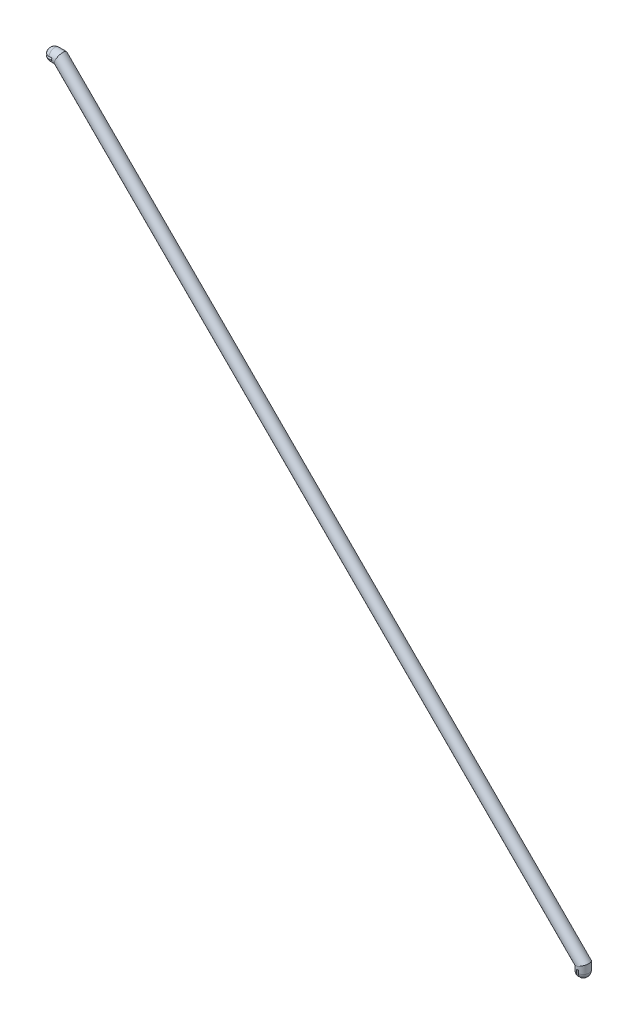
SolidWorks part; units mm, degrees
ref_plane "Front Plane" through (0, 0, 0) normal (0, 0, 1) x (1, 0, 0)
ref_plane "Top Plane" through (0, 0, 0) normal (0, 1, 0) x (1, 0, 0)
ref_plane "Right Plane" through (0, 0, 0) normal (1, 0, 0) x (0, 0, -1)
sketch "Sketch1" plane through (0, 0, 0) normal (0, 0, 1) x (1, 0, 0)
  line L0 (177.3813, -177.3813) -> (-177.3813, 177.3813)
  line L1 (-177.3813, 177.3813) -> (-181.3813, 177.3813)
  line L2 (177.3813, -177.3813) -> (177.3813, -181.3813)
  line L5 (177.3813, -177.3813) -> (177.3813, -182.3813) construction
  line L6 (177.3813, -182.3813) -> (-182.3813, -182.3813) construction
  line L7 (-182.3813, -182.3813) -> (-182.3813, 177.3813) construction
  line L8 (-182.3813, 177.3813) -> (-177.3813, 177.3813) construction
  point P4 (0, 0)
  dimension "D1" = 135
  dimension "D2" = 4
  dimension "D3" = 5
  dimension "D4" = 5
  dimension "D5" = 508.7811
ref_plane "Plane1" through (0, 0, 0) normal (-0.7071, 0.7071, 0) x (0, 0, 1)
sketch "Sketch2" plane through (0, 0, 0) normal (-0.7071, 0.7071, 0) x (0, 0, 1)
  circle A0 centre (0, 0) radius 4
  dimension "D1" = 8
sweep "Sweep1" add profiles "Sketch2" path "Sketch1"
ref_plane "Plane2" through (0, -181.3813, 0) normal (0, -1, 0) x (-1, 0, 0)
sketch "Sketch4" plane through (0, -181.3813, 0) normal (0, -1, 0) x (1, 0, 0)
  line L0 (177.3813, 4) -> (177.3813, -4)
  arc A0 (177.3813, -4) -> (177.3813, 4) centre (177.3813, 0) ccw
  circle A1 centre (177.3813, 0) radius 4 construction
revolve "Revolve7" add sketch "Sketch4" angle 180 about L0
sketch "Sketch6" plane through (0, -181.3813, 0) normal (0, -1, 0) x (-1, 0, 0)
  line L1 (-178.1313, 4) -> (-176.6313, 4)
  line L2 (-178.1313, 4) -> (-178.1313, -4)
  line L3 (-178.1313, -4) -> (-176.6313, -4)
  line L4 (-176.6313, 4) -> (-176.6313, -4)
  circle A0 centre (-177.3813, 0) radius 4 construction
  circle A1 centre (-177.3813, 0) radius 4 construction
  point P8 (-177.3813, 4)
  dimension "1.5" = 1.5
extrude "Cut-Extrude1" cut sketch "Sketch6" along normal blind 10 and the other way blind 2
ref_plane "Plane3" through (177.3813, 0, 0) normal (1, 0, 0) x (0, 0, -1)
sketch "Sketch8" plane through (177.3813, 0, 0) normal (1, 0, 0) x (0, 0, -1)
  line L0 (-3.9291, -181.3813) -> (3.9291, -181.3813) construction
  circle A0 centre (0, -182.3103) radius 0.75
  arc A1 (-3.9291, -181.3813) -> (3.9291, -181.3813) centre (0, -181.3813) ccw construction
  point P4 (0, -181.3813)
  point P8 (0, -185.3103)
  dimension "D1" = 1.5
  dimension "D2" = 3
extrude "Cut-Extrude2" cut sketch "Sketch8" against normal blind 1.5 and the other way blind 1.5 contours A0
mirror "Mirror1" about plane through (0, 0, 0) normal (-0.7071, 0.7071, 0) of "Revolve7", "Cut-Extrude1", "Cut-Extrude2"
